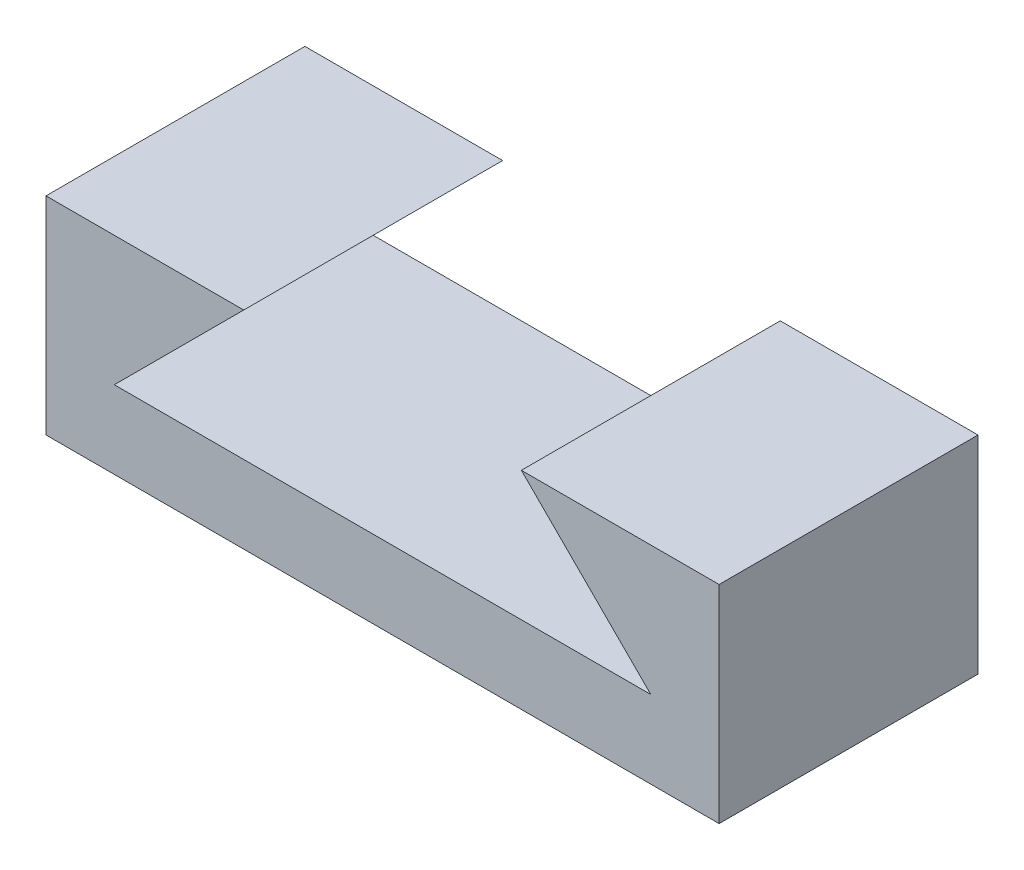
SolidWorks part; units mm, degrees
ref_plane "Alzado" through (0, 0, 0) normal (0, 0, 1) x (1, 0, 0)
ref_plane "Planta" through (0, 0, 0) normal (0, 1, 0) x (1, 0, 0)
ref_plane "Vista lateral" through (0, 0, 0) normal (1, 0, 0) x (0, 0, -1)
sketch "Croquis1" plane through (0, 0, 0) normal (0, 0, 1) x (1, 0, 0)
  line L0 (-10.2973, 4.6148) -> (9.7027, 4.6148) construction
  line L1 (-10.2973, 4.6148) -> (-10.2973, 0.6148) construction
  line L2 (-10.2973, 0.6148) -> (-5.2973, 0.6148) construction
  line L3 (-5.2973, 0.6148) -> (-10.2973, -4.3852) construction
  line L4 (-10.2973, -4.3852) -> (9.7027, -4.3852) construction
  line L5 (9.7027, -4.3852) -> (4.7027, 0.6148) construction
  line L6 (4.7027, 0.6148) -> (9.7027, 0.6148) construction
  line L7 (9.7027, 0.6148) -> (9.7027, 4.6148) construction
  line L8 (-10.2973, 0.4648) -> (-5.6594, 0.4648)
  line L9 (-5.6594, 0.4648) -> (-10.6594, -4.5352)
  line L10 (-10.6594, -4.5352) -> (10.0649, -4.5352)
  line L11 (10.0649, -4.5352) -> (5.0649, 0.4648)
  line L12 (5.0649, 0.4648) -> (9.7027, 0.4648)
  line L13 (-10.2973, 0.4648) -> (-13.2973, 0.4648)
  line L14 (-13.2973, 0.4648) -> (-13.2973, -7.5352)
  line L15 (-13.2973, -7.5352) -> (12.7027, -7.5352)
  line L16 (-0.2973, -7.5352) -> (-0.2973, -4.5352) construction
  line L17 (12.7027, 0.4648) -> (12.7027, -7.5352)
  line L18 (9.7027, 0.4648) -> (12.7027, 0.4648)
  dimension "D1" = 20
  dimension "D2" = 4
  dimension "D3" = 20
  dimension "D6" = 5
  dimension "D7" = 5
  dimension "D9" = 3
  dimension "D10" = 3
  dimension "D8" = 0.15
extrude "Saliente-Extruir1" add sketch "Croquis1" along normal blind 10
